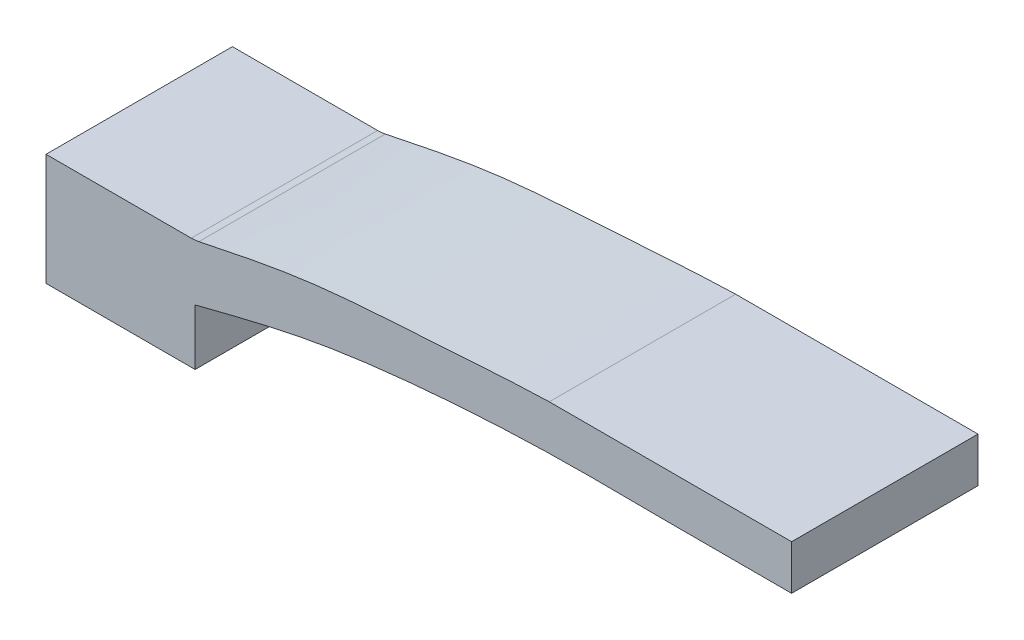
SolidWorks part; units mm, degrees
ref_plane "Front Plane" through (0, 0, 0) normal (0, 0, 1) x (1, 0, 0)
ref_plane "Top Plane" through (0, 0, 0) normal (0, 1, 0) x (1, 0, 0)
ref_plane "Right Plane" through (0, 0, 0) normal (1, 0, 0) x (0, 0, -1)
sketch "Sketch1" plane through (0, 0, 0) normal (0, 1, 0) x (1, 0, 0)
  line L1 (0, 0) -> (200, 0)
  line L2 (0, 0) -> (0, 50)
  line L3 (0, 50) -> (200, 50)
  line L4 (200, 0) -> (200, 50)
  point P5 (0, 0)
  dimension "D1" = 200
  dimension "D2" = 50
extrude "Boss-Extrude1" add sketch "Sketch1" along normal blind 40
sketch "Sketch3" plane through (0, 0, 0) normal (0, 0, 1) x (1, 0, 0)
  line L0 (0, 40) -> (0, 0) construction
  line L1 (0, 0) -> (200, 0) construction
  line L4 (200, 40) -> (200, 0) construction
  line L6 (0, 40) -> (200, 40) construction
  point P0 (40, 15)
  point P1 (170, 28)
  point P10 (70, 22)
  point P11 (100, 26)
  point P12 (135, 28)
  point P13 (0, 0)
  point P14 (0, 0)
  point P21 (200, 28)
  dimension "D1" = 40
  dimension "D2" = 15
  dimension "D3" = 30
  dimension "D4" = 12
  dimension "D5" = 7
  dimension "D6" = 4
  dimension "D7" = 2
  dimension "D8" = 30
  dimension "D9" = 30
  dimension "D10" = 35
curve "Curve4"
sketch "Sketch9" plane through (0, 0, 0) normal (0, 0, 1) x (1, 0, 0)
  line L0 (40, 15) -> (40, 0)
  line L1 (40, 0) -> (200, 0)
  line L2 (200, 0) -> (200, 28)
  line L3 (0, 0) -> (200, 0) construction
  spline S0 degree 3 poles (-479.859, 869.2449) (-157.285, -123.55) (-45.0309, 8.7046) (101.5695, 26.4847) (134.9726, 28.4303) (376.8151, 24.6603) (606.0954, 66.0996) (840.1462, -740.2477) knots -2.147345 -2.147345 -2.147345 -2.147345 0.191188 0.379023 0.596595 0.813813 4.880452 4.880452 4.880452 4.880452 only from (40, 15) to (200, 28) construction
  spline S1 degree 3 poles (40, 15) (49.9566, 17.5546) (69.6952, 22.6189) (101.5695, 26.4847) (134.9726, 28.4303) (168.3351, 27.9102) (190.0005, 27.9716) (200, 28) knots 0 0 0 0 0.191188 0.379023 0.596595 0.813813 1 1 1 1
  point P8 (0, 0)
  point P9 (0, 0)
  point P11 (0, 0)
  point P13 (0, 0)
  point P14 (200, 30)
  point P15 (0, 0)
extrude "Cut-Extrude1" cut sketch "Sketch9" against normal through all
sketch "Sketch10" plane through (0, 0, 0) normal (0, 0, 1) x (1, 0, 0)
  line L0 (0, 40) -> (200, 40) construction
  point P0 (40, 30)
  point P1 (70, 35.5)
  point P2 (100, 38)
  point P3 (135, 40)
  point P4 (170, 40)
  point P5 (0, 0)
  point P7 (0, 0)
  point P8 (0, 0)
  point P9 (17.3825, 22.8701)
  point P12 (0, 0)
  point P14 (0, 0)
  point P16 (0, 0)
  point P19 (0, 0)
  dimension "D1" = 15
  dimension "D2" = 2
  dimension "D3" = 5.5
curve "Curve5"
sketch "Sketch11" plane through (0, 0, 0) normal (0, 0, 1) x (1, 0, 0)
  line L0 (40, 30) -> (0, 30)
  line L1 (0, 30) -> (0, 40)
  line L2 (0, 40) -> (170, 40)
  spline S2 degree 3 poles (-409.7199, 923.1663) (-152.5193, -102.1907) (-39.6307, 30.2533) (101.6659, 37.9916) (274.9965, 51.2187) (442.0762, -41.1878) (558.244, 961.4913) knots -2.510924 -2.510924 -2.510924 -2.510924 0.233428 0.463826 0.732131 4.224006 4.224006 4.224006 4.224006 only from (40, 30) to (170, 40) construction
  spline S3 degree 3 poles (40, 30) (49.9657, 32.0906) (69.7677, 36.2447) (101.6659, 37.9916) (134.9619, 40.5325) (158.327, 40.1774) (170, 40) knots 0 0 0 0 0.233428 0.463826 0.732131 1 1 1 1
  point P4 (0, 0)
  point P8 (0, 0)
  line M8 (0, 40) -> (0, 0)
extrude "Cut-Extrude2" cut sketch "Sketch11" against normal through all contours L0 S3 L2 M8
fillet "Fillet3" radius 10 1 edges at (40, 30, -25)
